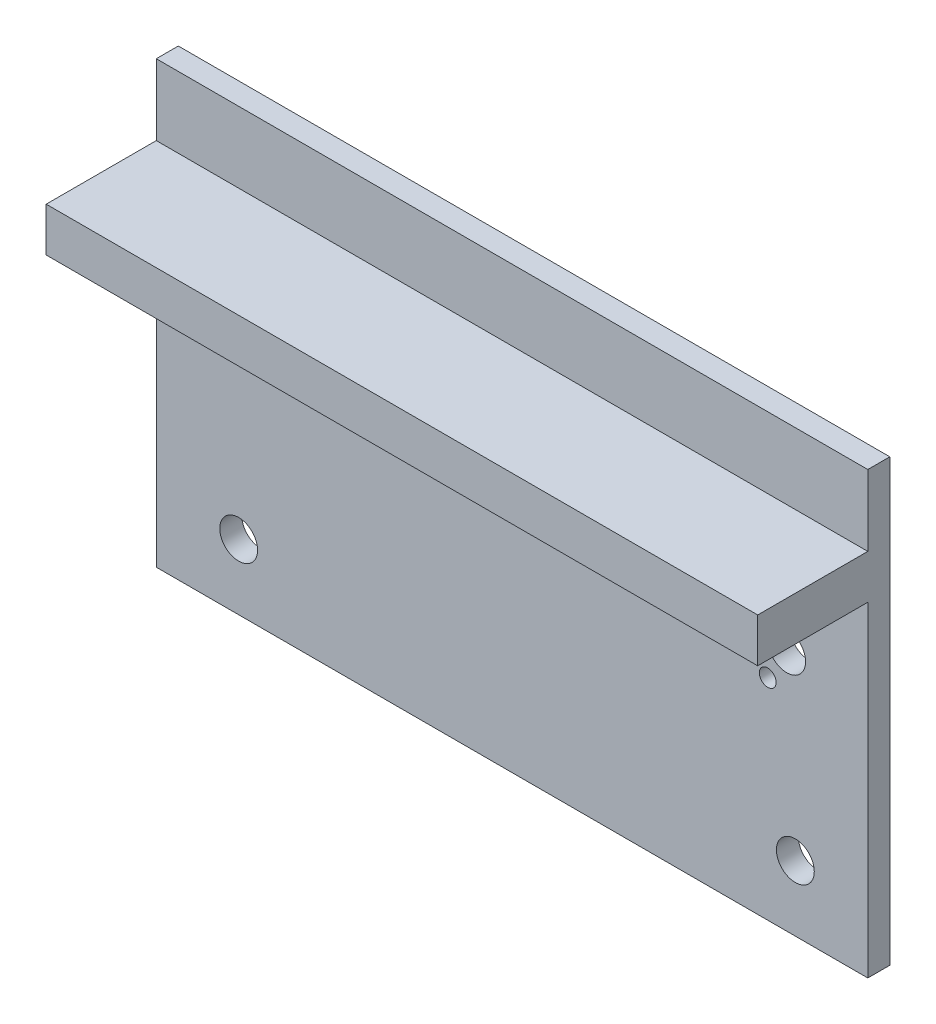
SolidWorks part; units mm, degrees
ref_plane "Plan de face" through (0, 0, 0) normal (0, 0, 1) x (1, 0, 0)
ref_plane "Plan de dessus" through (0, 0, 0) normal (0, 1, 0) x (1, 0, 0)
ref_plane "Plan de droite" through (0, 0, 0) normal (1, 0, 0) x (0, 0, -1)
sketch "Esquisse14" plane through (0, 0, 0) normal (0, 0, 1) x (1, 0, 0)
  line L1 (-2.884, -1.9022) -> (-2.884, -41.9022) construction
  line L2 (-67.5139, -1.9022) -> (-2.884, -1.9022)
  line L3 (-67.5139, -1.9022) -> (-67.5139, -41.9022)
  line L4 (-67.5139, -41.9022) -> (-2.884, -41.9022)
  line L5 (-2.884, -1.9022) -> (-2.884, -41.9022)
  line L9 (-2.884, -1.9022) -> (-67.5139, -1.9022) construction
  line L11 (-2.884, -41.9022) -> (-67.5139, -41.9022) construction
  line L12 (-67.5139, -1.9022) -> (-67.5139, -41.9022) construction
  circle A0 centre (-10.2538, -19.8511) radius 1.7192
  circle A1 centre (-9.465, -35.9658) radius 1.7192
  circle A2 centre (-58.9987, -18.6952) radius 1.7192
  circle A3 centre (-60.0303, -35.9658) radius 1.7192
  circle A4 centre (-11.973, -22.8188) radius 0.7629
  dimension "D1" = 40
extrude "Boss.-Extru.1" add sketch "Esquisse14" against normal blind 2
sketch "Esquisse15" plane through (0, 0, 0) normal (0, 0, 1) x (1, 0, 0)
  line L0 (-2.884, -1.9022) -> (-2.884, -8.3436) construction
  line L1 (-2.884, -41.9022) -> (-2.884, -1.9022) construction
  line L2 (-2.884, -8.3436) -> (-67.5139, -8.3436)
  line L3 (-67.5139, -1.9022) -> (-67.5139, -41.9022) construction
  line L4 (-67.5139, -8.3436) -> (-67.5139, -12.3436)
  line L5 (-67.5139, -12.3436) -> (-2.884, -12.3436)
  line L6 (-2.884, -12.3436) -> (-2.884, -8.3436)
extrude "Boss.-Extru.2" add sketch "Esquisse15" along normal blind 10
